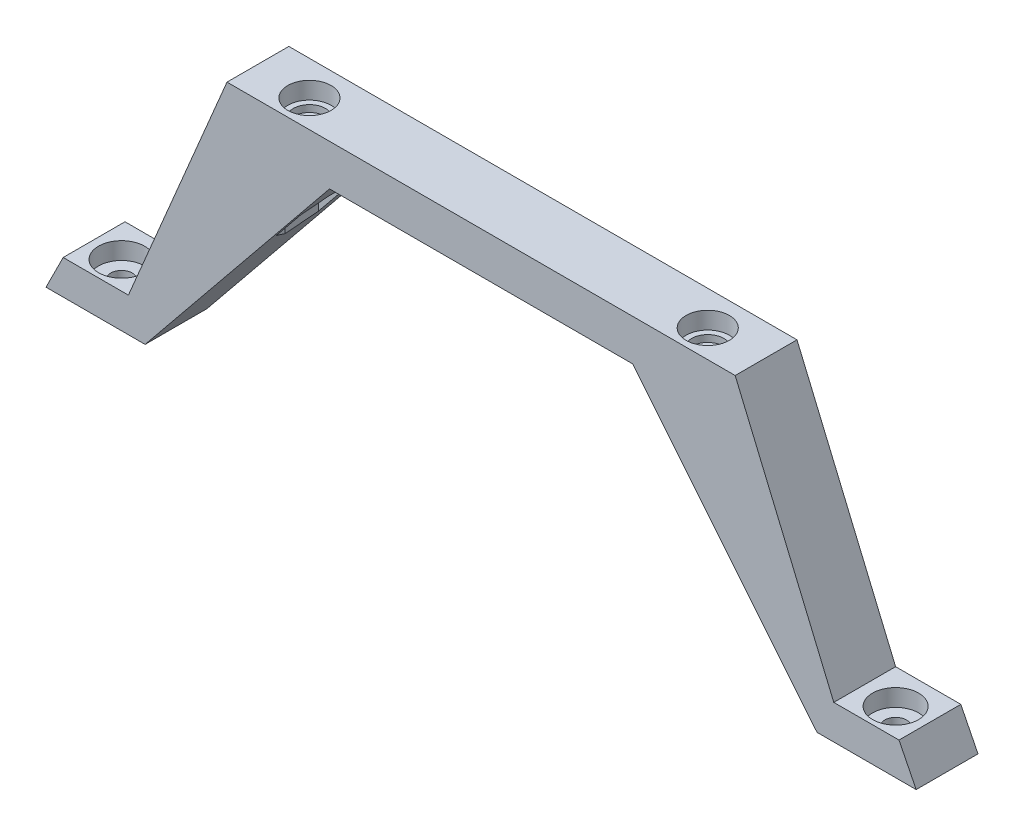
SolidWorks part; units mm, degrees
ref_plane "前视基准面" through (0, 0, 0) normal (0, 0, 1) x (1, 0, 0)
ref_plane "上视基准面" through (0, 0, 0) normal (0, 1, 0) x (1, 0, 0)
ref_plane "右视基准面" through (0, 0, 0) normal (1, 0, 0) x (0, 0, -1)
sketch "草图1" plane through (0, 0, 0) normal (0, 0, 1) x (1, 0, 0)
  line L0 (33.8113, 38.6957) -> (33.8113, 7.0528) construction
  line L1 (-3.1887, 13.0528) -> (33.8113, 13.0528)
  line L2 (-17.6144, -25.9913) -> (-15.1144, -25.9913)
  line L3 (-15.1144, -25.9913) -> (11.742, 7.0528)
  line L4 (33.8113, 13.0528) -> (33.8113, 7.0528)
  line L5 (15.602, 7.0528) -> (11.742, 7.0528)
  line L6 (-27.0458, -20.9913) -> (-17.5487, -20.9913)
  line L7 (33.8113, 7.0528) -> (15.602, 7.0528)
  line L8 (-17.6144, -25.9913) -> (-29.5458, -25.9913)
  line L11 (-17.5487, -20.9913) -> (-3.1887, 13.0528)
  line L14 (-27.0458, -20.9913) -> (-29.5458, -25.9913)
  point P0 (33.8113, 10.0528)
  point P7 (-17.6144, -10.6613)
  point P10 (-16.1887, -12.9472)
  point P11 (-17.5487, -15.6613)
extrude "凸台-拉伸1" add sketch "草图1" along normal blind 10
ref_plane "基准面3" through (33.8113, 0, 0) normal (1, 0, 0) x (0, 0, -1)
mirror "镜向1" about plane through (33.8113, 13.0528, 10) normal (-1, 0, 0) of "凸台-拉伸1"
ref_plane "基准面1" through (0, 0, 5) normal (0, 0, 1) x (1, 0, 0)
sketch "草图5" plane through (0, 0, 5) normal (0, 0, 1) x (1, 0, 0)
  line L0 (33.8113, 20.2752) -> (33.8113, -16.9928) construction
  line L1 (70.8113, 13.0528) -> (-3.1887, 13.0528) construction
  line L2 (7.9613, 13.0528) -> (7.9613, 10.5528)
  line L3 (7.9613, 10.5528) -> (7.1613, 10.5528)
  line L4 (7.1613, 10.5528) -> (7.1613, 9.5528)
  line L5 (7.1613, 9.5528) -> (6.3613, 9.5528)
  line L6 (4.8113, 13.0528) -> (4.8113, 2.5746) construction
  line L7 (4.8113, 13.0528) -> (7.9613, 13.0528)
  line L8 (6.3613, 9.5528) -> (4.8113, 9.5528)
  line L9 (4.8113, 9.5528) -> (4.8113, 13.0528)
  point P2 (4.8113, 13.0528)
  point P3 (62.8113, 13.0274)
  point P6 (7.9613, 13.0528)
  point P13 (6.3613, 9.5528)
  dimension "D2" = 29
  dimension "D3" = 3.15
revolve "切除-旋转7" cut sketch "草图5" angle 360 about L9
sketch "草图7" plane through (0, 9.5528, 0) normal (0, 1, 0) x (1, 0, 0)
  circle A0 centre (4.8113, -5) radius 1.55
  dimension "D1" = 3.1
extrude "切除-拉伸1" cut sketch "草图7" against normal through all
ref_plane "基准面2" through (0, -5.9472, 0) normal (0, 1, 0) x (1, 0, 0)
sketch "草图8" plane through (0, -5.9472, 0) normal (0, 1, 0) x (1, 0, 0)
  line L1 (8.3331, -5) -> (6.5722, -1.95)
  line L2 (6.5722, -1.95) -> (3.0504, -1.95)
  line L3 (3.0504, -1.95) -> (1.2895, -5)
  line L4 (1.2895, -5) -> (3.0504, -8.05)
  line L5 (3.0504, -8.05) -> (6.5722, -8.05)
  line L6 (6.5722, -8.05) -> (8.3331, -5)
  circle A0 centre (4.8113, -5) radius 3.05 construction
  dimension "D1" = 6.1
extrude "切除-拉伸2" cut sketch "草图8" along normal blind 8.5
sketch "草图14" plane through (0, -20.9913, 0) normal (0, 1, 0) x (1, 0, 0)
  line L0 (-17.5487, -10) -> (-17.5487, 0) construction
  line L3 (-17.5487, -10) -> (-27.0458, -10) construction
  circle A0 centre (-22.5487, -5) radius 1.575
  point P6 (-22.7418, -10)
  point P7 (-22.8792, -10)
  point P8 (-22.7524, -5.1823)
  dimension "D1" = 5
  dimension "D2" = 5
extrude "切除-拉伸10" cut sketch "草图14" against normal blind 10
sketch "草图15" plane through (0, -20.9913, 0) normal (0, 1, 0) x (1, 0, 0)
  circle A0 centre (-22.5487, -5) radius 3.35
extrude "切除-拉伸11" cut sketch "草图15" against normal blind 2.5
mirror "镜向3" about plane through (33.8113, 0, 0) normal (1, 0, 0) of "切除-拉伸2", "切除-拉伸1", "切除-旋转7", "切除-拉伸10", "切除-拉伸11"
sketch "草图19" plane through (0, 13.0528, 0) normal (0, 1, 0) x (1, 0, 0)
  line L4 (97.1684, -10) -> (97.1684, -9.004)
  line L5 (97.1684, -9.004) -> (-29.5458, -9.004)
  line L6 (-29.5458, -9.004) -> (-29.5458, -10)
  line L17 (-29.5458, -10) -> (97.1684, -10)
extrude "切除-拉伸14" cut sketch "草图19" against normal through all
